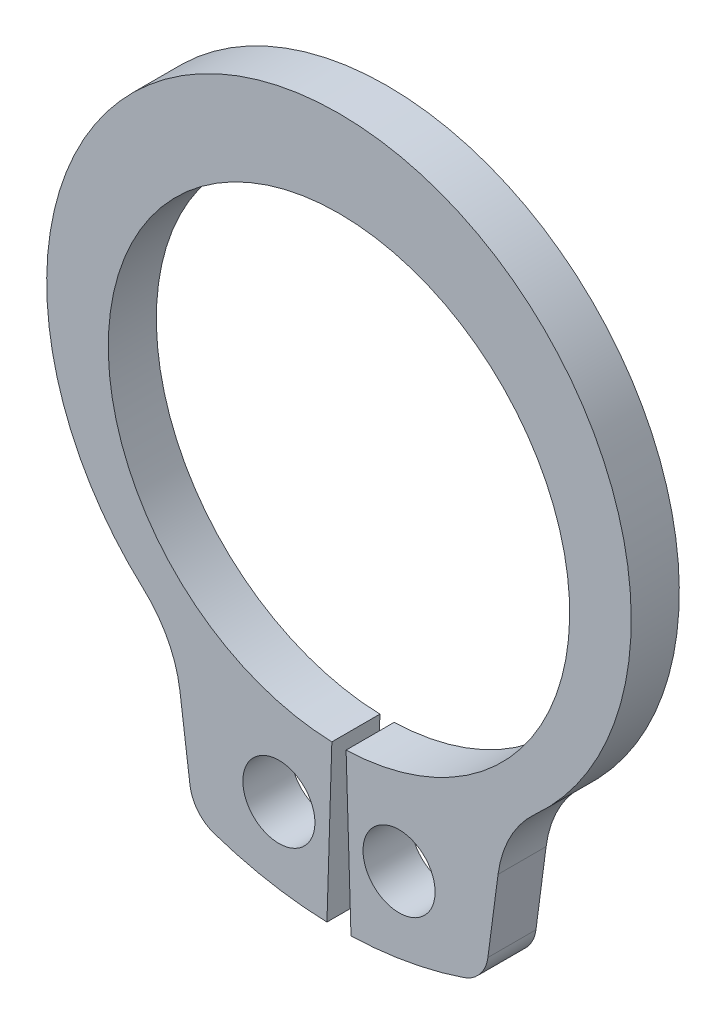
SolidWorks part; units mm, degrees
ref_plane "Plane1" through (0, 0, 0) normal (0, 0, 1) x (1, 0, 0)
ref_plane "Plane2" through (0, 0, 0) normal (0, 1, 0) x (1, 0, 0)
ref_plane "Plane3" through (0, 0, 0) normal (1, 0, 0) x (0, 0, -1)
other "Configuration Table"
sketch "Clipboard" plane through (0, 0, 0) normal (0, 0, 1) x (1, 0, 0)
  line L0 (0, 0) -> (1.8, 0)
  line L1 (0, 0) -> (0, 0.9)
  line L2 (0, 0) -> (0, -3.3)
  circle A0 centre (0, 0) radius 0.75
  circle A1 centre (0, 0) radius 5
  dimension "HoleDia" = 1.5
  dimension "SmallSection" = 1.3
sketch "BodySke" plane through (0, 0, 0) normal (0, 0, 1) x (1, 0, 0)
  line L0 (-1.5431, 0) -> (1.5431, 0) construction
  line L1 (0, 0) -> (0, 6.6) construction
  line L2 (0.1481, -4.7977) -> (0.25, -8.0961)
  line L3 (-0.1481, -4.7977) -> (-0.25, -8.0961)
  line L4 (0, 0) -> (5.6861, -5.7688) construction
  line L5 (0, 0) -> (-5.6861, -5.7688) construction
  line L7 (3.3097, -5.4559) -> (3.0984, -7.0605)
  line L8 (-3.3097, -5.4559) -> (-3.0984, -7.0605)
  circle A0 centre (0, 0) radius 4.8 construction
  arc A1 (0.1481, -4.7977) -> (-0.1481, -4.7977) centre (0, 0) ccw
  arc A2 (4.0013, -4.0595) -> (-4.0013, -4.0595) centre (0, 0.5193) ccw construction
  arc A3 (0.25, -8.0961) -> (2.5951, -7.673) centre (0, 0) ccw
  arc A4 (4.0784, -3.991) -> (3.3097, -5.4559) centre (5.6861, -5.7688) ccw
  arc A5 (-3.3097, -5.4559) -> (-4.0784, -3.991) centre (-5.6861, -5.7688) ccw
  arc A6 (-2.5951, -7.673) -> (-0.25, -8.0961) centre (0, 0) ccw
  arc A7 (4.0784, -3.991) -> (-4.0784, -3.991) centre (0, 0.5193) ccw
  arc A8 (-3.2816, -5.6686) -> (3.2816, -5.6686) centre (0, 0) ccw construction
  circle A9 centre (1.25, -6.4296) radius 0.75
  circle A10 centre (-1.25, -6.4296) radius 0.75
  arc A11 (3.0984, -7.0605) -> (2.5951, -7.673) centre (2.3548, -6.9626) cw
  arc A12 (-3.0984, -7.0605) -> (-2.5951, -7.673) centre (-2.3548, -6.9626) ccw
  point P28 (3.0395, -7.5081)
  point P31 (-3.0395, -7.5081)
  dimension "LugRad" = 13.5
  dimension "HoleOffsetRad" = 11.75
  dimension "HoleDia" = 2
  dimension "D3" = 0.75
  dimension "LargeRad" = 12.1
  dimension "SmallRad" = 10.8
  dimension "SmallAngle" = 61.378
  dimension "D2" = 15
  dimension "HoleSpacing" = 3.2
  dimension "Gap" = 0.6
extrude "Body" add sketch "BodySke" against normal blind 1
sketch "NotSke" plane through (0, 0, 0) normal (0, 0, 1) x (1, 0, 0)
  line L0 (1.25, -5.6796) -> (1.25, -7.1796)
  line L1 (1.25, -7.1796) -> (-1.25, -7.1796)
  line L2 (-1.25, -7.1796) -> (-1.25, -5.6796)
  line L3 (-1.25, -5.6796) -> (1.25, -5.6796)
  circle A0 centre (1.25, -6.4296) radius 0.75 construction
  circle A1 centre (-1.25, -6.4296) radius 0.75 construction
extrude "Notch" [suppressed] cut sketch "NotSke" against normal through all
sketch "UnlSke" plane through (0, 0, 0) normal (0, 0, 1) x (1, 0, 0)
  line L0 (-2.4461, -7.7218) -> (-1.4495, -4.5759)
  line L1 (2.4461, -7.7218) -> (1.4495, -4.5759)
  arc A0 (1.4495, -4.5759) -> (-1.4495, -4.5759) centre (0, 0) ccw
  arc A1 (2.4461, -7.7218) -> (-2.4461, -7.7218) centre (0, 0) ccw
  arc A2 (0.25, -8.0961) -> (2.5951, -7.673) centre (0, 0) ccw construction
  arc A3 (0.1481, -4.7977) -> (-0.1481, -4.7977) centre (0, 0) ccw construction
  circle A4 centre (-1.25, -6.4296) radius 0.75 construction
  circle A5 centre (1.25, -6.4296) radius 0.75 construction
extrude "Unlug" [suppressed] add sketch "UnlSke" against normal through all
equation "' \"ShaftDia@Clipboard\" = 3"
equation "' \"Thickness@Body\" = 0.4"
equation "' \"GrooveDia@BodySke\" = 2.8"
equation "' \"LugSection@Clipboard\" = 1.9"
equation "' \"LargeSection@Clipboard\" = 0.8"
equation "' \"HoleDia@Clipboard\" = 1.0"
equation "' \"ShaftDia@Clipboard\" = 10"
equation "' \"Thickness@Body\" = 1.0"
equation "' \"GrooveDia@BodySke\" = 9.6"
equation "' \"LugSection@Clipboard\" = 3.3"
equation "' \"LargeSection@Clipboard\" = 1.8"
equation "' \"HoleDia@Clipboard\" = 1.5"
equation "\"SmallSection@Clipboard\" = \"LargeSection@Clipboard\" * 0.5"
equation "\"Gap@BodySke\" =  \"Thickness@Body\" / 2"
equation "\"LargeRad@BodySke\" =  \"GrooveDia@BodySke\" / 2 +  \"LargeSection@Clipboard\""
equation "\"SmallRad@BodySke\" =  \"GrooveDia@BodySke\" / 2 +  \"SmallSection@Clipboard\""
equation "\"LugRad@BodySke\" = \"GrooveDia@BodySke\" / 2 + \"LugSection@Clipboard\""
equation "\"HoleOffsetRad@BodySke\" = (  \"ShaftDia@Clipboard\" / 2 + \"LugRad@BodySke\" ) / 2"
equation "\"HoleSpacing@BodySke\" = \"Gap@BodySke\"  * 2 +  \"HoleDia@Clipboard\""
equation "\"HoleDia@BodySke\" =  \"HoleDia@Clipboard\""
equation "\"SmallAngle@BodySke\" = atn(\"HoleSpacing@BodySke\" / 2 / sqr(\"HoleOffsetRad@BodySke\"  * \"HoleOffsetRad@BodySke\" - (\"HoleSpacing@BodySke\" / 2) * (\"HoleSpacing@BodySke\" / 2) ))  * 7 *  (\"LargeRad@BodySke\" / \"SmallRad@BodySke\")* ( 180 / 3.141593)"
